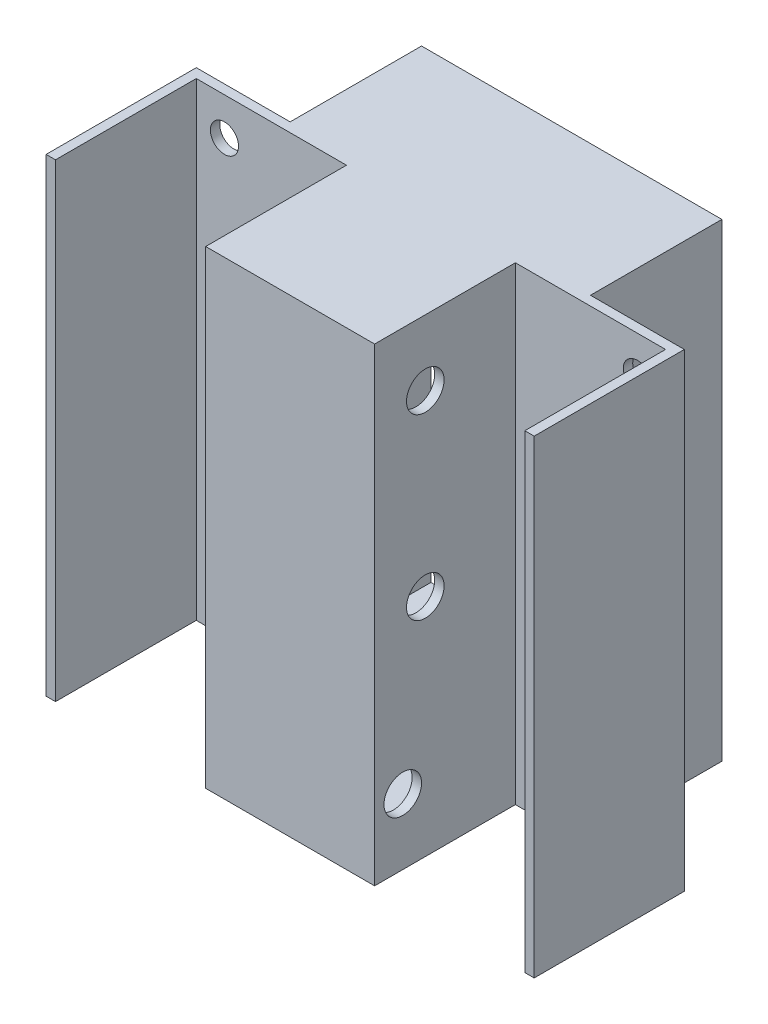
SolidWorks part; units mm, degrees
ref_plane "Plan de face" through (0, 0, 0) normal (0, 0, 1) x (1, 0, 0)
ref_plane "Plan de dessus" through (0, 0, 0) normal (0, 1, 0) x (1, 0, 0)
ref_plane "Plan de droite" through (0, 0, 0) normal (1, 0, 0) x (0, 0, -1)
sketch "Esquisse1" plane through (0, 0, 0) normal (0, 0, 1) x (1, 0, 0)
  line L1 (0, 0) -> (-90, 0)
  line L2 (0, 0) -> (0, 250)
  line L3 (0, 250) -> (-90, 250)
  line L4 (-90, 0) -> (-90, 250)
  dimension "D1" = 250
  dimension "D2" = 90
extrude "Boss.-Extru.1" add sketch "Esquisse1" along normal blind 5
sketch "Esquisse2" plane through (0, 0, 0) normal (0, 0, -1) x (-1, 0, 0)
  line L0 (5, 245) -> (5, 5)
  line L1 (0, 250) -> (90, 250)
  line L2 (0, 250) -> (0, 0)
  line L3 (0, 0) -> (90, 0)
  line L4 (90, 250) -> (90, 0)
  line L5 (5, 5) -> (85, 5)
  line L6 (85, 245) -> (85, 5)
  line L7 (5, 245) -> (85, 245)
  dimension "D1" = 5
extrude "Boss.-Extru.2" add sketch "Esquisse2" along normal blind 70
sketch "Esquisse3" plane through (0, 0, -70) normal (0, 0, -1) x (-1, 0, 0)
  line L0 (90, 250) -> (0, 250) construction
  line L1 (6.0255, 250) -> (-80, 250)
  line L2 (5, 245) -> (5, 5)
  line L3 (-15, 0) -> (-80, 0)
  line L4 (-80, 250) -> (-80, 0)
  line L5 (85, 245) -> (5, 245) construction
  line L6 (45, 245) -> (5, 245)
  line L7 (45, 245) -> (45, 250)
  line L8 (45, 250) -> (6.0255, 250)
  line L9 (5, 245) -> (5, 5) construction
  line L10 (5, 5) -> (85, 5) construction
  line L11 (45, 5) -> (5, 5)
  line L12 (45, 5) -> (45, 0)
  line L13 (45, 0) -> (-15, 0)
  line L14 (0, 250) -> (0, 0) construction
  dimension "D1" = 80
extrude "Boss.-Extru.3" add sketch "Esquisse3" along normal blind 5
mirror "Symétrie1" about plane through (-45, 245, -75) normal (1, 0, 0) of "Boss.-Extru.3"
sketch "Esquisse4" plane through (-90, 0, 0) normal (-1, 0, 0) x (0, 0, 1)
  line L0 (5, 250) -> (5, 0) construction
  line L1 (5, 250) -> (-70, 250) construction
  line L2 (5, 0) -> (-70, 0) construction
  circle A0 centre (-22, 215) radius 30
  circle A1 centre (-22, 215) radius 10
  circle A2 centre (-22, 120) radius 10
  circle A3 centre (-10, 35) radius 10
  circle A4 centre (-22, 25) radius 10 [skipped]
  dimension "D1" = 27
  dimension "D3" = 60
  dimension "D4" = 20
  dimension "D6" = 20
  dimension "D2" = 35
  dimension "D7" = 15
  dimension "D8" = 35
  dimension "D5" = 3
extrude "Enlèv. mat.-Extru.2" cut sketch "Esquisse4" against normal through all contours A1 | A2 | A3
sketch "Esquisse5" plane through (80, 0, 0) normal (1, 0, 0) x (0, 0, -1)
  line L1 (75, 250) -> (-5, 250)
  line L2 (75, 250) -> (75, 0)
  line L3 (75, 0) -> (-5, 0)
  line L4 (-5, 250) -> (-5, 0)
extrude "Boss.-Extru.4" add sketch "Esquisse5" along normal blind 5
sketch "Esquisse6" plane through (-170, 0, 0) normal (-1, 0, 0) x (0, 0, 1)
  line L1 (-75, 250) -> (5, 250)
  line L2 (-75, 250) -> (-75, 0)
  line L3 (-75, 0) -> (5, 0)
  line L4 (5, 250) -> (5, 0)
extrude "Boss.-Extru.5" add sketch "Esquisse6" along normal blind 5
sketch "Esquisse7" plane through (0, 0, -75) normal (0, 0, -1) x (-1, 0, 0)
  line L0 (175, 250) -> (-85, 250) construction
  line L1 (-35, 250) -> (125, 250)
  line L2 (-35, 250) -> (-35, 0)
  line L3 (-35, 0) -> (125, 0)
  line L4 (125, 250) -> (125, 0)
  line L5 (-85, 0) -> (175, 0) construction
  line L6 (-85, 0) -> (-85, 250) construction
  line L7 (175, 250) -> (175, 0) construction
  line L8 (-30, 245) -> (120, 245)
  line L9 (120, 245) -> (120, 5)
  line L10 (-30, 5) -> (120, 5)
  line L11 (-30, 245) -> (-30, 5)
  dimension "D1" = 50
  dimension "D2" = 50
  dimension "D3" = 5
extrude "Boss.-Extru.6" add sketch "Esquisse7" along normal blind 70
sketch "Esquisse10" plane through (0, 0, -75) normal (0, 0, -1) x (-1, 0, 0)
  line L0 (-35, 250) -> (-85, 250) construction
  line L1 (175, 250) -> (125, 250) construction
  line L2 (175, 250) -> (175, 0) construction
  line L3 (-85, 0) -> (-85, 250) construction
  circle A0 centre (155, 230) radius 7.5
  circle A1 centre (-65, 230) radius 7.5
  circle A2 centre (-65, 160) radius 7.5
  circle A3 centre (155, 160) radius 7.5
  circle A4 centre (-65, 90) radius 7.5
  circle A5 centre (155, 90) radius 7.5
  circle A6 centre (-65, 20) radius 7.5
  circle A7 centre (155, 20) radius 7.5
  point P4 (-60, 250)
  dimension "D1" = 15
  dimension "D2" = 15
  dimension "D5" = 20
  dimension "D3" = 20
  dimension "D4" = 20
  dimension "D6" = 20
  dimension "D7" = 4
extrude "Enlèv. mat.-Extru.3" cut sketch "Esquisse10" against normal blind 50
sketch "Esquisse12" plane through (0, 0, 0) normal (0, -1, 0) x (1, 0, 0)
  line L0 (-125, -145) -> (-125, -75) construction
  line L1 (35, -145) -> (35, -75) construction
  line L2 (-75, -104.8689) -> (16.3849, -104.8689) construction
  line L3 (16.3849, -104.8689) -> (-113.6872, -104.8689) construction
  circle A0 centre (-15, -104.8689) radius 20
  circle A1 centre (-75, -104.8689) radius 20
  dimension "D1" = 40
  dimension "D2" = 40
  dimension "D3" = 50
  dimension "D4" = 50
extrude "Enlèv. mat.-Extru.4" cut sketch "Esquisse12" against normal blind 10
